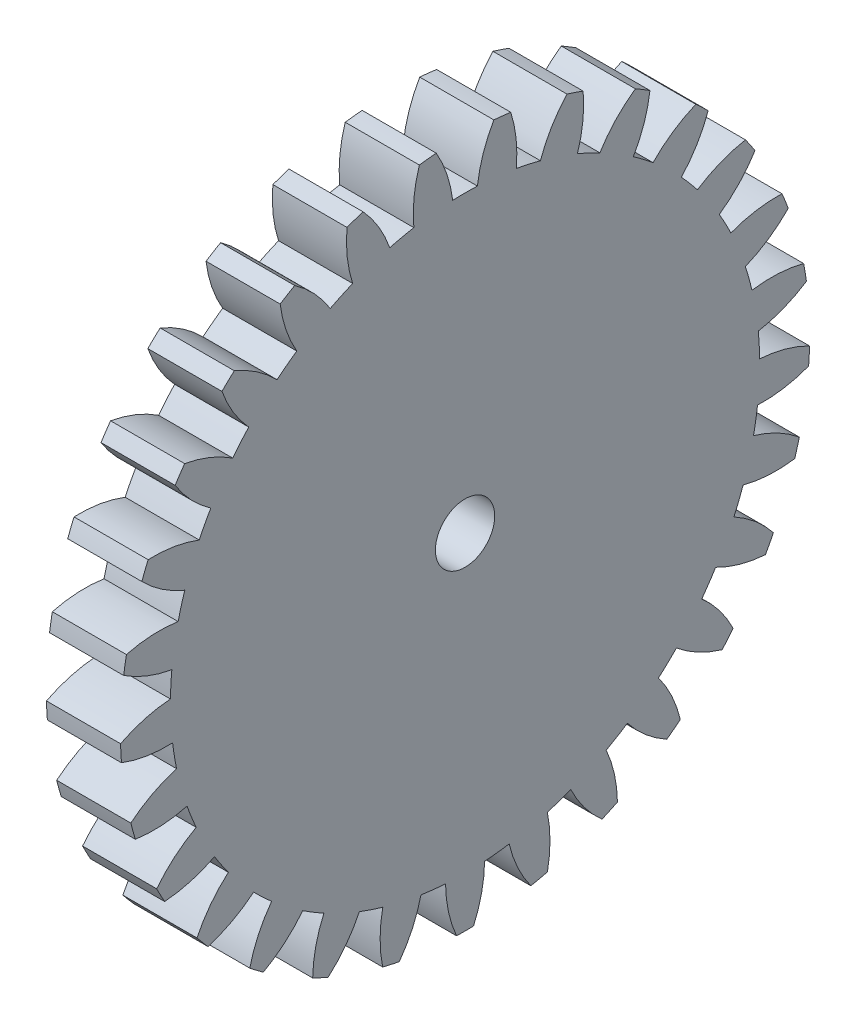
SolidWorks part; units mm, degrees
ref_plane "Plane1" through (0, 0, 0) normal (0, 0, 1) x (1, 0, 0)
ref_plane "Plane2" through (0, 0, 0) normal (0, 1, 0) x (1, 0, 0)
ref_plane "Plane3" through (0, 0, 0) normal (1, 0, 0) x (0, 0, -1)
sketch "HoldingSke" plane through (0, 0, 0) normal (0, 1, 0) x (1, 0, 0)
  line L0 (0, 0) -> (0.5831, -0.3232)
  line L1 (-15, 0) -> (100, 0) construction
  line L2 (0, 0) -> (-2.1039, 2.3779)
  line L3 (0, 0) -> (-11.863, 4.5341)
  line L4 (0, 0) -> (7.5532, 4.1868)
  line L5 (0, 0) -> (-46.8476, -17.4728)
  line L6 (0, 0) -> (-4.1448, -2.7965)
  line L7 (-2.1039, 2.3779) -> (8.6586, 51.2059)
  line L8 (-76.2, 54.61) -> (-75.5, 54.61)
  line L9 (-67.7845, 28.3722) -> (-49.3413, 33.142)
  line L10 (-76.2, 71.12) -> (104.1128, 71.12)
  line L11 (0, 0) -> (-5, 0)
  line L12 (-76.2, 101.6) -> (-76.147, 101.6)
  line L13 (24.9733, 27.94) -> (52.9518, 28.4284)
  line L14 (24.9733, 27.94) -> (24.9743, 27.94)
  line L15 (24.9733, 27.94) -> (100.4006, 29.5858)
  line L16 (-63.627, -1.5) -> (-12.827, -1.5)
  circle A0 centre (0, 0) radius 2
  circle A1 centre (0, 0) radius 19.874
  circle A2 centre (0, 0) radius 37.5
  circle A3 centre (0, 0) radius 2
  dimension "MHD" = 39.748
  dimension "Hub_dia" = 75
  dimension "Bore" = 4
  dimension "MBD" = 4
  dimension "Num_teeth" = 29
  dimension "Pitch" = 0.6667
  dimension "Overall_len" = 50
  dimension "Show_teeth" = 29
  dimension "Thickness" = 5
  dimension "OAL" = 50.0001
  dimension "T_dim" = 0.7
  dimension "Ap" = 14.5
  dimension "H" = 19.05
  dimension "Pitch_radius" = 180.3128
  dimension "Width" = 5
  dimension "Backlash" = 0.053
  dimension "Addendum_fac" = 1
  dimension "Dedendum_fac" = 1.25
  dimension "Clearance_fac" = 0.25
  dimension "Dedendum_add" = 0.001
  dimension "Module" = 1.5
sketch "BasProSke" plane through (0, 0, 0) normal (0, 1, 0) x (1, 0, 0)
  line L0 (-10, 0) -> (60, 0) construction
  line L1 (0, 0) -> (0, 23.25)
  line L2 (0, 0) -> (5, 0)
  line L3 (5, 0) -> (5, 23.25)
  line L4 (5, 23.25) -> (0, 23.25)
  dimension "Thickness" = 5
  dimension "Diameter" = 46.5
revolve "Base-Revolve" add sketch "BasProSke" angle 360 about L0
sketch "TooCutSke" plane through (0, 0, 0) normal (1, 0, 0) x (0, 0, -1)
  line L1 (0, 0) -> (0, 107) construction
  line L2 (0, 0) -> (-1.2702, 21.7129) construction
  line L3 (0, 0) -> (-4.6973, 43.1912) construction
  line L4 (-1.2702, 21.7129) -> (-2.3487, 21.5956) construction
  arc A0 (0.8342, 19.8565) -> (-0.8342, 19.8565) centre (0, 0) ccw
  arc A1 (1.957, 23.193) -> (-1.957, 23.193) centre (0, 0) ccw
  circle A2 centre (0, 0) radius 21.75 construction
  circle A3 centre (0, 0) radius 21.0572 construction
  arc A4 (-0.8342, 19.8565) -> (-1.957, 23.193) centre (-9.4707, 18.8072) ccw
  arc A5 (1.957, 23.193) -> (0.8342, 19.8565) centre (9.4707, 18.8072) ccw
  dimension "Root_dia" = 39.748
  dimension "Overcut_dia" = 46.5508
  dimension "Pitch_dia" = 43.5
  dimension "Base_dia" = 42.1144
  dimension "Flank_rad" = 8.7
  dimension "Half_ang" = 6.207
  dimension "Half_CT" = 1.0848
extrude "ToothCut" cut sketch "TooCutSke" along normal through all
fillet "Breaks" [suppressed] radius 0.03
fillet "RootFillets" [suppressed] radius 0.376
pattern_circular "TeethCuts" count 29 every 12.414 about axis through (-10, 0, 0) along (1, 0, 0) of "ToothCut", "RootFillets", "Breaks"
sketch "HubNeaOneSke" plane through (0, 0, 0) normal (-1, 0, 0) x (0, 0, 1)
  circle A0 centre (0, 0) radius 19.874
  dimension "Diameter" = 39.748
extrude "HubNearOne" [suppressed] add sketch "HubNeaOneSke" along normal blind 45.0001
sketch "HubNeaBotSke" plane through (0, 0, 0) normal (-1, 0, 0) x (0, 0, 1)
  circle A0 centre (0, 0) radius 19.874
  dimension "Diameter" = 39.748
extrude "HubNearBoth" [suppressed] add sketch "HubNeaBotSke" along normal blind 22.5
ref_plane "FarPln" through (5, 0, 0) normal (1, 0, 0) x (0, 0, -1)
sketch "HubFarSke" plane through (5, 0, 0) normal (1, 0, 0) x (0, 0, -1)
  circle A0 centre (0, 0) radius 19.874
  dimension "Diameter" = 39.748
extrude "HubFar" [suppressed] add sketch "HubFarSke" along normal blind 22.5
sketch "BorSke" plane through (0, 0, 0) normal (1, 0, 0) x (0, 0, -1)
  circle A0 centre (0, 0) radius 2
  dimension "Diameter" = 4
extrude "Bore" cut sketch "BorSke" along normal mid plane 100.0001
sketch "KeySke" plane through (0, 0, 0) normal (1, 0, 0) x (0, 0, -1)
  line L0 (-0.8, 0) -> (-0.8, 2.7)
  line L1 (-0.8, 2.7) -> (0.8, 2.7)
  line L2 (0.8, 2.7) -> (0.8, 0)
  line L3 (0, 0) -> (0, 34) construction
  line L4 (-0.8, 0) -> (0.8, 0)
  dimension "Offset" = 2.7
  dimension "Width" = 1.6
extrude "Keyway" [suppressed] cut sketch "KeySke" along normal mid plane 100.0001
pattern_circular "Keyway2" [suppressed] count 2 every 90 about axis through (-10, 0, 0) along (1, 0, 0)
equation "' \"Module@HoldingSke\" = 6.35"
equation "' \"Num_teeth@HoldingSke\" = 12"
equation "' \"Ap@HoldingSke\" =  20"
equation "' \"Ap@HoldingSke\" = 20"
equation "' \"Width@HoldingSke\" = 0.5 * 25.4"
equation "' \"Hub_dia@HoldingSke\"= 1 * 25.4"
equation "' \"Hub_dia@HoldingSke\" = 1 * 25.4"
equation "' \"Overall_len@HoldingSke\" = 1.0 * 25.4"
equation "' \"Bore@HoldingSke\" = 0.75 * 25.4"
equation "' \"T_dim@HoldingSke\" = 0.1 * 25.4"
equation "' \"Width@KeySke\" = 0.25 * 25.4"
equation "' \"Show_teeth@HoldingSke\" = 13"
equation "' \"Backlash@HoldingSke\" = 0.009 * 25.4"
equation "' \"Addendum_fac@HoldingSke\" = 1.0"
equation "' \"Dedendum_fac@HoldingSke\" = 1.25"
equation "' \"Dedendum_add@HoldingSke\" = 0.00005 * 25.4"
equation "' \"Clearance_fac@HoldingSke\" = 0.25"
equation "\"Pitch@HoldingSke\" = 1 / \"Module@HoldingSke\""
equation "\"Overcut_dia@TooCutSke\" = (\"Num_teeth@HoldingSke\" + 2 * \"Addendum_fac@HoldingSke\") / \"Pitch@HoldingSke\" + 0.002 * 25.4"
equation "\"Pitch_dia@TooCutSke\" = \"Num_teeth@HoldingSke\" / \"Pitch@HoldingSke\""
equation "\"Base_dia@TooCutSke\" = \"Num_teeth@HoldingSke\" / \"Pitch@HoldingSke\" * cos((\"Ap@HoldingSke\"  * 3.14159265 / 180))"
equation "\"Root_dia@TooCutSke\" = (\"Num_teeth@HoldingSke\" + 2) / \"Pitch@HoldingSke\" - 2 * (\"Addendum_fac@HoldingSke\" + \"Dedendum_fac@HoldingSke\") / \"Pitch@HoldingSke\" - \"Dedendum_add@HoldingSke\" * 2"
equation "\"Half_ang@TooCutSke\" = 180 / \"Num_teeth@HoldingSke\""
equation "\"Half_CT@TooCutSke\" = \"Num_teeth@HoldingSke\" / \"Pitch@HoldingSke\" * sin((3.14159265 / 2 / \"Num_teeth@HoldingSke\")) / 2 - 7 * \"Backlash@HoldingSke\" / 4"
equation "\"Flank_rad@TooCutSke\" = \"Num_teeth@HoldingSke\" / \"Pitch@HoldingSke\" / 5"
equation "\"Radius@RootFillets\" = \"Clearance_fac@HoldingSke\" / \"Pitch@HoldingSke\" + \"Dedendum_add@HoldingSke\""
equation "\"Break_rad@Breaks\" = 0.02 / \"Pitch@HoldingSke\""
equation "\"Thickness@HoldingSke\" = \"Width@HoldingSke\""
equation "\"OAL@HoldingSke\" = \"Thickness@HoldingSke\""
equation "\"MHD@HoldingSke\" = (\"Num_teeth@HoldingSke\" + 2) / \"Pitch@HoldingSke\" - 2 * (\"Addendum_fac@HoldingSke\" + \"Dedendum_fac@HoldingSke\")  / \"Pitch@HoldingSke\" - \"Dedendum_add@HoldingSke\" * 2"
equation "\"MBD@HoldingSke\" = (\"Num_teeth@HoldingSke\" + 2) / \"Pitch@HoldingSke\" - 2 * (\"Addendum_fac@HoldingSke\" + \"Dedendum_fac@HoldingSke\")  / \"Pitch@HoldingSke\" - \"Dedendum_add@HoldingSke\" * 2 - 0.002 * 25.4"
equation "\"MHD@HoldingSke\" = ((sgn( \"MHD@HoldingSke\" - \"Hub_dia@HoldingSke\" )-1)*( \"MHD@HoldingSke\" - \"Hub_dia@HoldingSke\" ))/-2+ \"Hub_dia@HoldingSke\""
equation "\"MBD@HoldingSke\" = ((sgn( \"MBD@HoldingSke\" - \"Bore@HoldingSke\" )-1)*( \"MBD@HoldingSke\" - \"Bore@HoldingSke\" ))/-2+ \"Bore@HoldingSke\""
equation "\"OAL@HoldingSke\" = ((sgn( \"OAL@HoldingSke\" - \"Overall_len@HoldingSke\" )+1)*( \"OAL@HoldingSke\" - \"Overall_len@HoldingSke\" ))/2 + \"Overall_len@HoldingSke\" + 0.000002 * 25.4"
equation "\"Num_teeth@TeethCuts\" = int( \"Show_teeth@HoldingSke\" ) + 1"
equation "\"Num_teeth@TeethCuts\" = ((sgn( \"Num_teeth@TeethCuts\" - \"Num_teeth@HoldingSke\" )-1)*( \"Num_teeth@TeethCuts\" - \"Num_teeth@HoldingSke\" ))/-2+ \"Num_teeth@HoldingSke\""
equation "\"Num_teeth@TeethCuts\" = ((sgn( \"Num_teeth@TeethCuts\" - 2.0)+1)*( \"Num_teeth@TeethCuts\" - 2.0))/2 +2.0"
equation "\"Angle@TeethCuts\" = 360.0 / \"Num_teeth@HoldingSke\""
equation "\"Diameter@BasProSke\" = (\"Num_teeth@HoldingSke\" + 2 * \"Addendum_fac@HoldingSke\") / \"Pitch@HoldingSke\""
equation "\"Thickness@BasProSke\"  = \"Thickness@HoldingSke\""
equation "' \"Fillet_rad@BasProSke\" =  \"Thickness@HoldingSke\" * 0.05"
equation "' \"Fillet_rad@BasProSke\" = \"Thickness@HoldingSke\" * 0.05"
equation "\"MHD@HoldingSke\" = ((sgn( \"MHD@HoldingSke\" - \"Root_dia@TooCutSke\" )-1)*( \"MHD@HoldingSke\" - \"Root_dia@TooCutSke\" ))/-2+ \"Root_dia@TooCutSke\""
equation "\"Diameter@HubNeaOneSke\" = \"MHD@HoldingSke\""
equation "\"Length@HubNearOne\" = \"OAL@HoldingSke\" - \"Thickness@BasProSke\""
equation "\"Diameter@HubNeaBotSke\" = \"MHD@HoldingSke\""
equation "\"Length@HubNearBoth\" = ( \"OAL@HoldingSke\" - \"Thickness@BasProSke\" ) / 2.0"
equation "\"Thickness@FarPln\" = \"Thickness@BasProSke\""
equation "\"Diameter@HubFarSke\" = \"MHD@HoldingSke\""
equation "\"Length@HubFar\" = ( \"OAL@HoldingSke\" - \"Thickness@BasProSke\" ) / 2.0"
equation "\"Diameter@BorSke\" = \"MBD@HoldingSke\""
equation "\"D1@Bore\" = \"OAL@HoldingSke\" * 2.0"
equation "\"D1@Keyway\" = \"OAL@HoldingSke\" * 2.0"
equation "\"Offset@KeySke\" = \"T_dim@HoldingSke\" + \"MBD@HoldingSke\" / 2.0"
